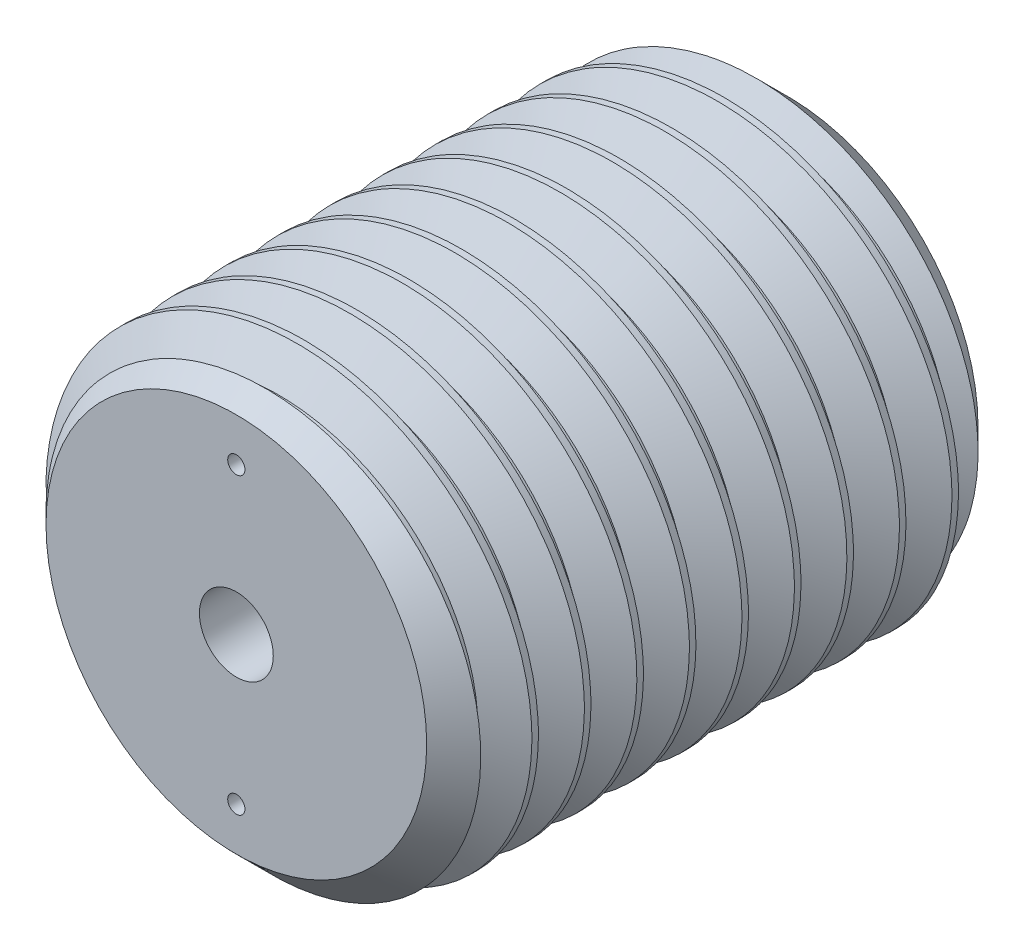
SolidWorks part; units mm, degrees
ref_plane "Front Plane" through (0, 0, 0) normal (0, 0, 1) x (1, 0, 0)
ref_plane "Top Plane" through (0, 0, 0) normal (0, 1, 0) x (1, 0, 0)
ref_plane "Right Plane" through (0, 0, 0) normal (1, 0, 0) x (0, 0, -1)
sketch "Sketch1" plane through (0, 0, 0) normal (0, 0, 1) x (1, 0, 0)
  circle A0 centre (0, 0) radius 15.875
  dimension "Diameter" = 31.75
extrude "Boss-Extrude1" add sketch "Sketch1" along normal mid plane 38.1
chamfer "Chamfer1" distance 2.7214 angle 45 2 edges at (15.875, 0, -19.05) (15.875, 0, 19.05)
sketch "Sketch4" plane through (0, 0, 19.05) normal (0, 0, 1) x (1, 0, 0)
  circle A1 centre (0, 0) radius 15.875
  circle A2 centre (0, 0) radius 15.875
  dimension "D1" = 0
curve "Helix/Spiral1" pitch 3.6286 height 41.7286 turns 11.5 parameters "Pitch"=3.6286
sketch "Sketch5" plane through (0, 0, 0) normal (1, 0, 0) x (0, 0, -1)
  line L0 (-20.8643, 13.5182) -> (-20.4107, 13.5182)
  line L1 (-20.4107, 13.5182) -> (-19.05, 15.875) construction
  line L2 (-19.05, 15.875) -> (-22.225, 15.875) construction
  line L3 (-22.225, 15.875) -> (-20.8643, 13.5182) construction
  line L4 (-20.6375, 13.5182) -> (-20.6375, 15.875) construction
  line L5 (-19.05, 15.875) -> (-19.05, -15.875) construction
  line L6 (-19.7304, 14.6966) -> (-21.5446, 14.6966) construction
  line L7 (-22.225, 15.875) -> (-22.3716, 16.129) construction
  line L8 (-22.3716, 16.129) -> (-18.9034, 16.129)
  line L9 (-18.9034, 16.129) -> (-19.05, 15.875) construction
  line L10 (-22.3716, 16.129) -> (-20.8643, 13.5182)
  line L11 (-20.4107, 13.5182) -> (-18.9034, 16.129)
  dimension "D1" = 60
  dimension "D3" = 1.8143
  dimension "D4" = 0.254
sweep "Cut-Sweep1" cut profiles "Sketch5" path "Helix/Spiral1"
sketch "Sketch6" plane through (0, 0, 0) normal (1, 0, 0) x (0, 0, -1)
  line L0 (-19.05, 0) -> (19.05, 0) construction
  line L1 (-19.05, 15.875) -> (19.05, 15.875)
  line L2 (-19.05, 15.875) -> (-19.05, -15.875)
  line L3 (-19.05, -15.875) -> (19.05, -15.875)
  line L4 (19.05, 15.875) -> (19.05, -15.875)
  point P4 (2.7214, -15.875)
  point P5 (-2.7214, -15.875)
  dimension "D1" = 38.1
  dimension "D2" = 31.75
  dimension "D3" = 16.3286
  dimension "D4" = 16.3286
hole_wizard "1/4-20 Tapped Hole1" positions "Sketch8" profile "Sketch7" tap size "1/4-20" standard "ANSI Inch"
sketch "Sketch8" plane through (0, 0, 19.05) normal (0, 0, 1) x (1, 0, 0)
  point P0 (0, 0)
sketch "Sketch7" plane through (0, 0, 19.05) normal (1, 0, 0) x (0, -1, 0)
  line L0 (0, 0) -> (0, 13.4718)
  line L1 (0, 13.4718) -> (2.5527, 11.938)
  line L2 (2.5527, 11.938) -> (2.5527, 0)
  line L5 (2.5527, 0) -> (0, 0)
  line L10 (0, 13.4718) -> (-2.5527, 11.938) construction
  line L11 (0, -6.35) -> (0, 107.95) construction
  dimension "Tap Drill Dia." = 5.1054
  dimension "Tap Drill Depth" = 11.938
  dimension "Drill Angle" = 118
cosmetic thread "Hole Thread1" parameters "D1"=8.128, "D2"=6.35
sketch "Sketch9" plane through (0, 0, 19.05) normal (0, 0, 1) x (1, 0, 0)
  line L0 (0, 13.1536) -> (0, -13.1536) construction
  circle A0 centre (0, 0) radius 13.1536 construction
hole_wizard "3/64 (0.04688) Diameter Hole1" positions "Sketch11" profile "Sketch10" hole size "3/64" standard "ANSI Inch"
sketch "Sketch11" plane through (0, 0, 19.05) normal (0, 0, 1) x (1, 0, 0)
  line L0 (0, 13.1536) -> (0, -13.1536) construction
  point P0 (0, 10.16)
  point P4 (0, -10.16)
  dimension "D1" = 10.16
  dimension "D2" = 10.16
sketch "Sketch10" plane through (0, 10.16, 19.05) normal (1, 0, 0) x (0, -1, 0)
  line L0 (0, 0) -> (0, 2.8977)
  line L1 (0, 2.8977) -> (0.5954, 2.54)
  line L2 (0.5954, 2.54) -> (0.5954, 0)
  line L5 (0.5954, 0) -> (0, 0)
  line L10 (0, 2.8977) -> (-0.5954, 2.54) construction
  line L11 (0, -6.35) -> (0, 107.95) construction
  dimension "Hole Dia." = 1.1908
  dimension "Hole Depth" = 2.54
  dimension "Drill Angle" = 118
equation "\"D2@Sketch5\" = \"Pitch@Helix/Spiral1\"*.125"
equation "\"D3@Sketch5\" = \"Pitch@Helix/Spiral1\"*.5"
equation "\"D1@Chamfer1\" = \"Pitch@Helix/Spiral1\"*.75"
equation "\"D3@Helix/Spiral1\" = \"Length@Boss-Extrude1\"+\"Pitch@Helix/Spiral1\""
equation "\"D1@Sketch6\" = \"Length@Boss-Extrude1\""
equation "\"D2@Sketch6\" = \"Diameter@Sketch1\""
equation "\"D3@Sketch6\" = \"Pitch@Helix/Spiral1\"*4.5"
equation "\"D4@Sketch6\" = \"D3@Sketch6\""
